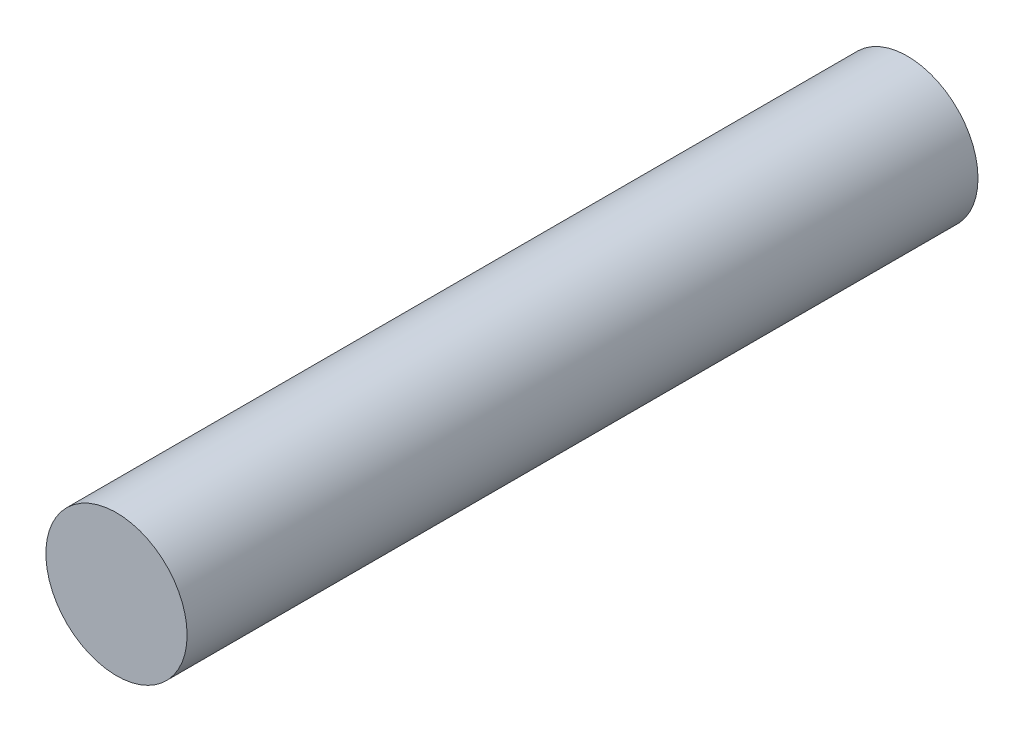
SolidWorks part; units mm, degrees
ref_plane "Alzado" through (0, 0, 0) normal (0, 0, 1) x (1, 0, 0)
ref_plane "Planta" through (0, 0, 0) normal (0, 1, 0) x (1, 0, 0)
ref_plane "Vista lateral" through (0, 0, 0) normal (1, 0, 0) x (0, 0, -1)
sketch "Croquis6" plane through (0, 0, 0) normal (0, 0, 1) x (1, 0, 0)
  circle A0 centre (0, 0) radius 2.5
  dimension "D1" = 5
extrude "Saliente-Extruir12" add sketch "Croquis6" along normal blind 28
scale "Escala1" scale about centroid uniform scaling yes scale factor 7
